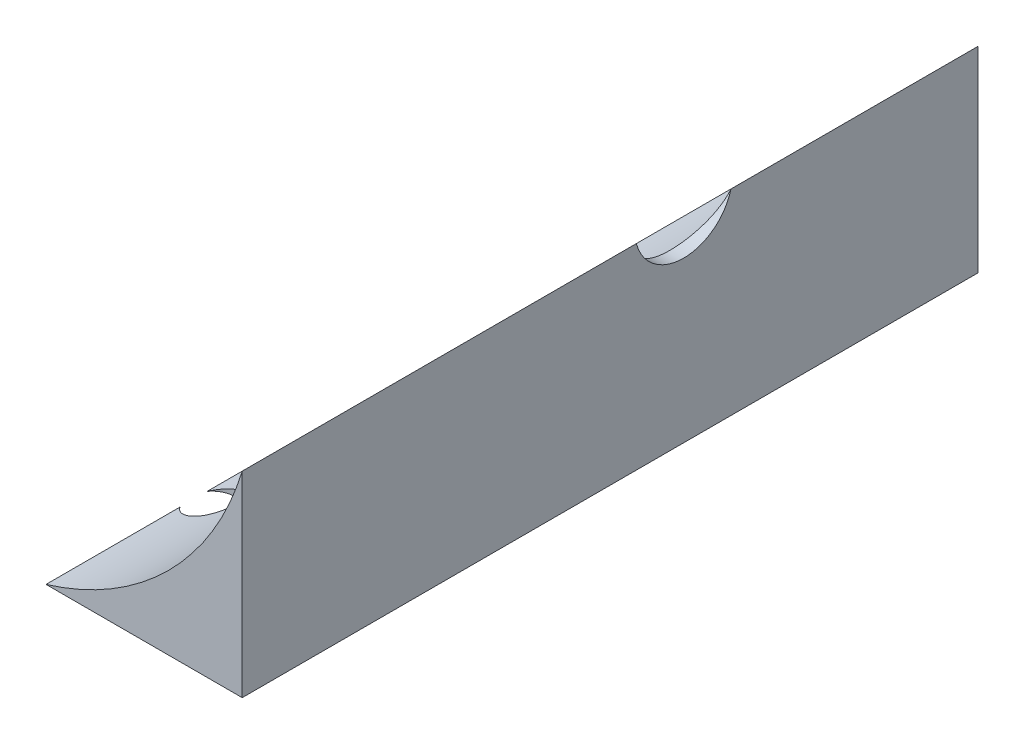
SolidWorks part; units mm, degrees
ref_plane "Front Plane" through (0, 0, 0) normal (0, 0, 1) x (1, 0, 0)
ref_plane "Top Plane" through (0, 0, 0) normal (0, 1, 0) x (1, 0, 0)
ref_plane "Right Plane" through (0, 0, 0) normal (1, 0, 0) x (0, 0, -1)
sketch "Sketch1" plane through (0, 0, 0) normal (0, 0, 1) x (1, 0, 0)
  line L0 (0, 0) -> (0, 20)
  line L1 (0, 0) -> (-20, 0)
  arc A0 (0, 20) -> (-20, 0) centre (-28.7083, 28.7083) cw
  dimension "D3" = 30
  dimension "D1" = 20
  dimension "D2" = 20
extrude "Boss-Extrude1" add sketch "Sketch1" along normal blind 75
sketch "Sketch2" plane through (0, 0, 0) normal (1, 0, 0) x (0, 0, -1)
  circle A0 centre (-30, 21.3) radius 5
extrude "Cut-Extrude1" cut sketch "Sketch2" against normal blind 10
sketch "Sketch4" plane through (0, 0, 0) normal (0, -1, 0) x (-1, 0, 0)
  circle A0 centre (18.1137, -59.964) radius 2.341
extrude "Cut-Extrude2" cut sketch "Sketch4" against normal blind 10
